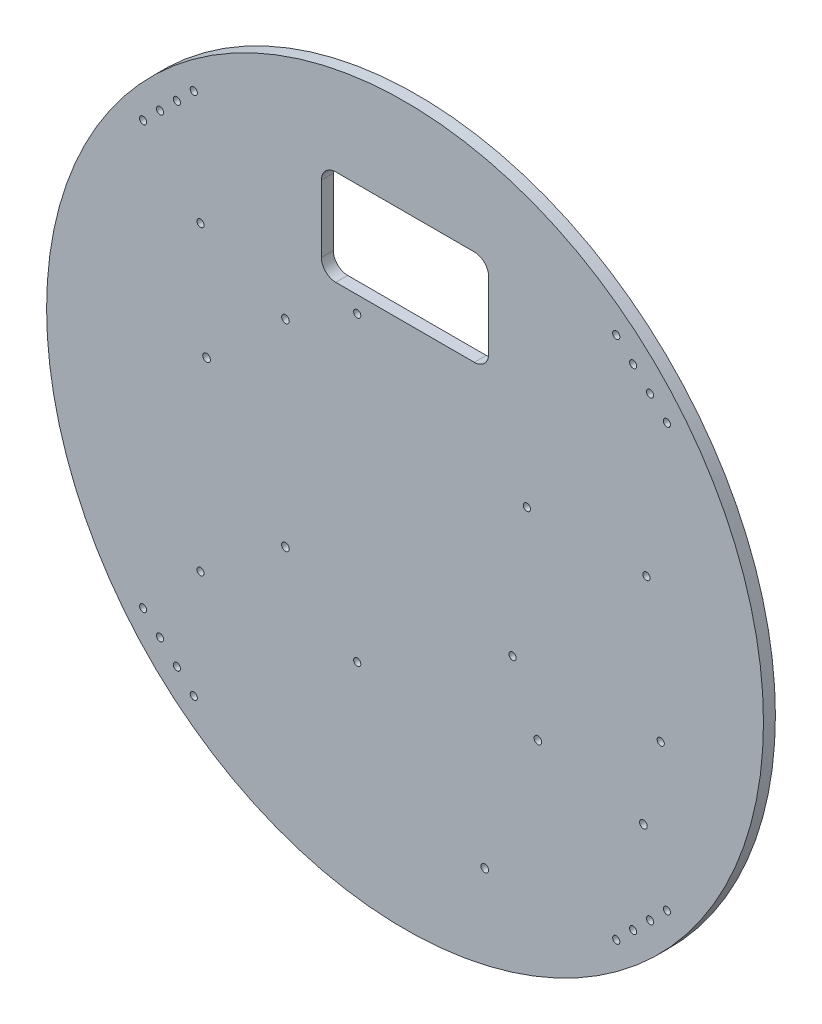
SolidWorks part; units mm, degrees
ref_plane "Plan de face" through (0, 0, 0) normal (0, 0, 1) x (1, 0, 0)
ref_plane "Plan de dessus" through (0, 0, 0) normal (0, 1, 0) x (1, 0, 0)
ref_plane "Plan de droite" through (0, 0, 0) normal (1, 0, 0) x (0, 0, -1)
sketch "Esquisse5" plane through (0, 0, 0) normal (0, 0, 1) x (1, 0, 0)
  circle A0 centre (0, 0) radius 150
  circle A1 centre (99.7392, -62.0496) radius 1.6
  circle A2 centre (55.5966, -53.6364) radius 1.6
  circle A3 centre (33.3808, -111.1522) radius 1.6
  circle A4 centre (-50.0437, -36.4182) radius 1.6
  circle A5 centre (-83.0637, 15.6518) radius 1.6
  circle A6 centre (-50.0437, 46.1318) radius 1.6
extrude "base" add sketch "Esquisse5" along normal blind 5
sketch "Esquisse8" plane through (0, 0, 5) normal (0, 0, 1) x (1, 0, 0)
  line L1 (-85.6, 63.115) -> (-20, 63.115) construction
  line L2 (-85.6, 63.115) -> (-85.6, -63.115) construction
  line L3 (-85.6, -63.115) -> (-20, -63.115) construction
  line L4 (-20, 63.115) -> (-20, -63.115) construction
  circle A0 centre (-85.6, 63.115) radius 1.5
  circle A1 centre (-20, 63.115) radius 1.5
  circle A2 centre (-85.6, -63.115) radius 1.5
  circle A3 centre (-20, -63.115) radius 1.5
  dimension "D1" = 65.6
  dimension "D2" = 126.23
  dimension "D3" = 63.115
  dimension "D4" = 20
extrude "fixation écran" cut sketch "Esquisse8" against normal through all
sketch "Esquisse9" plane through (0, 0, 5) normal (0, 0, 1) x (1, 0, 0)
  line L1 (45, 28.5) -> (107, 28.5) construction
  line L2 (45, 28.5) -> (45, -28.5) construction
  line L3 (45, -28.5) -> (107, -28.5) construction
  line L4 (107, 28.5) -> (107, -28.5) construction
  circle A1 centre (45, -28.5) radius 1.5
  circle A4 centre (107, -28.5) radius 1.5
  circle A5 centre (101, 28.5) radius 1.5
  circle A6 centre (51, 28.5) radius 1.5
  point P12 (76, 28.5)
  dimension "D5" = 50
  dimension "D1" = 57
  dimension "D2" = 62
  dimension "D3" = 28.5
  dimension "D4" = 45
  dimension "D6" = 25
extrude "fixation lidar" cut sketch "Esquisse9" against normal through all
sketch "Esquisse7" plane through (0, 0, 5) normal (0, 0, 1) x (1, 0, 0)
  line L1 (-35, 110) -> (35, 110)
  line L2 (-35, 110) -> (-35, 70)
  line L3 (-35, 70) -> (35, 70)
  line L4 (35, 110) -> (35, 70)
  dimension "D1" = 40
  dimension "D2" = 110
  dimension "D3" = 35
  dimension "D4" = 70
extrude "extrusion passage de cables " cut sketch "Esquisse7" against normal blind 5
fillet "Congé1" radius 6 4 edges at (-35, 110, 2.5) (-35, 70, 2.5) (35, 70, 2.5) (35, 110, 2.5)
sketch "Esquisse10" plane through (0, 0, 5) normal (0, 0, 1) x (1, 0, 0)
  circle A0 centre (-102.5305, 95.4594) radius 1.5
  circle A1 centre (-95.4594, 102.5305) radius 1.5
  circle A2 centre (95.4594, 102.5305) radius 1.5
  circle A3 centre (102.5305, 95.4594) radius 1.5
  circle A4 centre (102.5305, -95.4594) radius 1.5
  circle A5 centre (95.4594, -102.5305) radius 1.5
  circle A6 centre (-95.4594, -102.5305) radius 1.5
  circle A7 centre (-102.5305, -95.4594) radius 1.5
extrude "extrusion fixation paroi" cut sketch "Esquisse10" against normal through all
sketch "Esquisse11" plane through (0, 0, 5) normal (0, 0, 1) x (1, 0, 0)
  line L0 (95.4594, 102.5305) -> (35450.7985, -35252.8086) construction
  line L1 (102.5305, -95.4594) -> (-35252.8086, -35450.7985) construction
  line L2 (-95.4594, -102.5305) -> (-35450.7985, 35252.8086) construction
  line L3 (-95.4594, 102.5305) -> (-35450.7985, -35252.8086) construction
  circle A0 centre (-88.3883, 109.6016) radius 1.5
  circle A1 centre (-109.6016, 88.3883) radius 1.5
  circle A2 centre (-109.6016, -88.3883) radius 1.5
  circle A3 centre (-88.3883, -109.6016) radius 1.5
  circle A4 centre (88.3883, -109.6016) radius 1.5
  circle A5 centre (109.6016, -88.3883) radius 1.5
  circle A6 centre (109.6016, 88.3883) radius 1.5
  circle A7 centre (88.3883, 109.6016) radius 1.5
  circle A8 centre (-95.4594, 102.5305) radius 1.5 construction
  circle A9 centre (-102.5305, 95.4594) radius 1.5 construction
  circle A10 centre (-102.5305, -95.4594) radius 1.5 construction
  circle A11 centre (-95.4594, -102.5305) radius 1.5 construction
  circle A12 centre (102.5305, -95.4594) radius 1.5 construction
  circle A13 centre (95.4594, -102.5305) radius 1.5 construction
  circle A14 centre (95.4594, 102.5305) radius 1.5 construction
  circle A15 centre (102.5305, 95.4594) radius 1.5 construction
  dimension "D1" = 10
  dimension "D2" = 10
  dimension "D3" = 10
  dimension "D4" = 10
  dimension "D5" = 10
  dimension "D6" = 10
  dimension "D7" = 10
  dimension "D8" = 10
extrude "Enlèv. mat.-Extru.1" cut sketch "Esquisse11" against normal up to next
